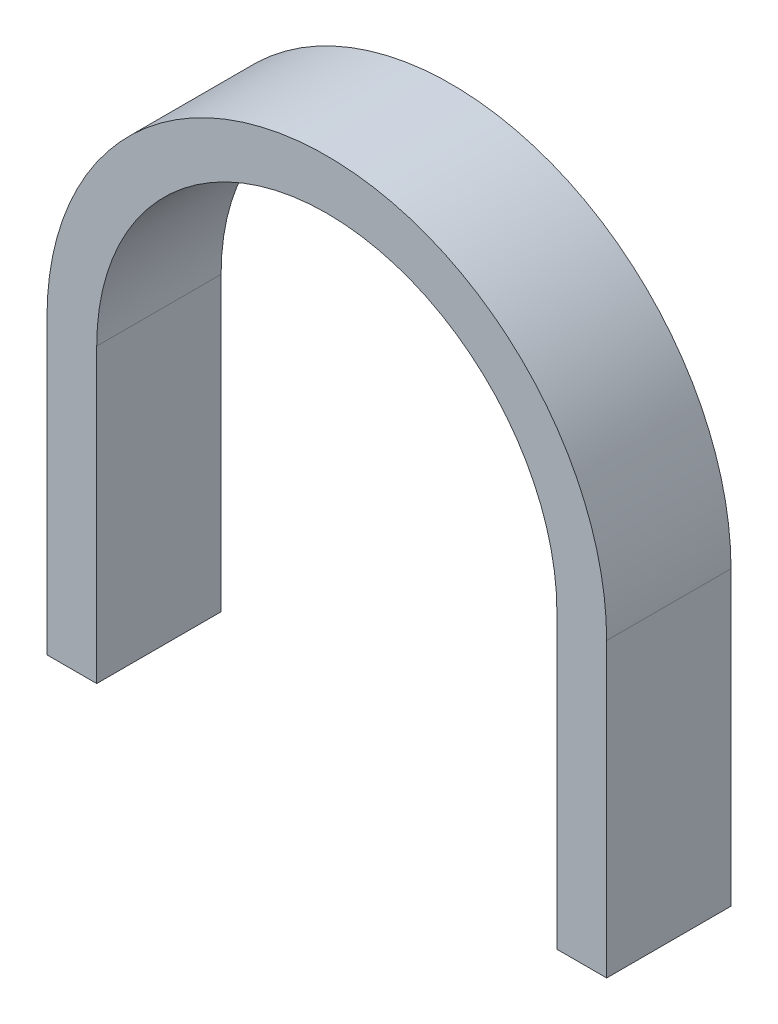
SolidWorks part; units mm, degrees
ref_plane "Front Plane" through (0, 0, 0) normal (0, 0, 1) x (1, 0, 0)
ref_plane "Top Plane" through (0, 0, 0) normal (0, 1, 0) x (1, 0, 0)
ref_plane "Right Plane" through (0, 0, 0) normal (1, 0, 0) x (0, 0, -1)
sketch "Sketch1" plane through (0, 0, 0) normal (0, 0, 1) x (1, 0, 0)
  line L0 (0, 0) -> (57.2179, 0) construction
  line L1 (18.5, 18.5) -> (18.5, 0)
  line L2 (-18.5, 18.5) -> (-18.5, 0)
  line L3 (22.5, 18.5) -> (22.5, 0)
  line L4 (-22.5, 18.5) -> (-22.5, 0)
  line L5 (22.5, 0) -> (18.5, 0)
  line L6 (-18.5, 0) -> (-22.5, 0)
  arc A0 (18.5, 18.5) -> (-18.5, 18.5) centre (0, 18.5) ccw
  arc A1 (22.5, 18.5) -> (-22.5, 18.5) centre (0, 18.5) ccw
  dimension "D1" = 37
  dimension "D2" = 4
extrude "Boss-Extrude1" add sketch "Sketch1" along normal blind 10
sketch "Sketch2" plane through (0, 0, 0) normal (0, -1, 0) x (1, 0, 0)
  line L4 (18.5, 0) -> (22.5, 0)
  line L5 (22.5, 0) -> (22.5, 10)
  line L6 (22.5, 10) -> (18.5, 10)
  line L7 (18.5, 10) -> (18.5, 0)
  line L8 (18.5, 0) -> (22.5, 0)
  line L9 (22.5, 0) -> (22.5, 10)
  line L10 (22.5, 10) -> (18.5, 10)
  line L11 (18.5, 10) -> (18.5, 0)
  line L12 (-22.5, 0) -> (-18.5, 0)
  line L13 (-18.5, 0) -> (-18.5, 10)
  line L14 (-18.5, 10) -> (-22.5, 10)
  line L15 (-22.5, 10) -> (-22.5, 0)
  line L16 (-22.5, 0) -> (-18.5, 0)
  line L17 (-18.5, 0) -> (-18.5, 10)
  line L18 (-18.5, 10) -> (-22.5, 10)
  line L19 (-22.5, 10) -> (-22.5, 0)
  dimension "D1" = 0
  dimension "D2" = 0
extrude "Boss-Extrude2" add sketch "Sketch2" along normal blind 5
